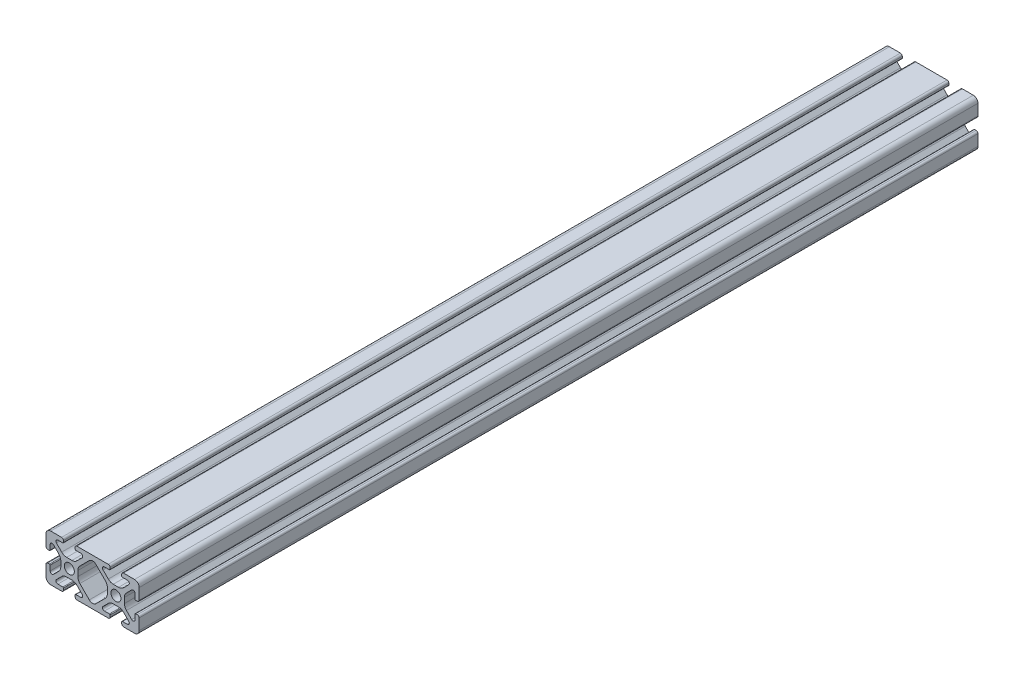
SolidWorks part; units mm, degrees
ref_plane "Alzado" through (0, 0, 0) normal (0, 0, 1) x (1, 0, 0)
ref_plane "Planta" through (0, 0, 0) normal (0, 1, 0) x (1, 0, 0)
ref_plane "Vista lateral" through (0, 0, 0) normal (1, 0, 0) x (0, 0, -1)
ref_plane "Plano1" through (0, 0, 20) normal (0, 0, 1) x (1, 0, 0)
sketch "Croquis1" plane through (0, 0, 20) normal (0, 0, 1) x (1, 0, 0)
  line L0 (32.5, 1.5) -> (32.5, 0.8)
  line L1 (33.3, 0) -> (38, 0)
  line L2 (40, 2) -> (40, 6.7)
  line L3 (39.2, 7.5) -> (38.5, 7.5)
  line L4 (38.2, 7.2) -> (38.2, 5.0824)
  line L5 (36.779, 4.4938) -> (34.5287, 6.7441)
  line L6 (33.65, 8.8654) -> (33.65, 11.1346)
  line L7 (34.5287, 13.2559) -> (36.779, 15.5062)
  line L8 (38.2, 14.9176) -> (38.2, 12.8)
  line L9 (38.5, 12.5) -> (39.2, 12.5)
  line L10 (40, 13.3) -> (40, 18)
  line L11 (38, 20) -> (33.3, 20)
  line L12 (32.5, 19.2) -> (32.5, 18.5)
  line L13 (32.8, 18.2) -> (34.9176, 18.2)
  line L14 (35.5062, 16.779) -> (33.2559, 14.5287)
  line L15 (31.1346, 13.65) -> (28.8654, 13.65)
  line L16 (26.7441, 14.5287) -> (24.4938, 16.779)
  line L17 (25.0824, 18.2) -> (27.2, 18.2)
  line L18 (27.5, 18.5) -> (27.5, 19.2)
  line L19 (26.7, 20) -> (13.3, 20)
  line L20 (12.5, 19.2) -> (12.5, 18.5)
  line L21 (12.8, 18.2) -> (14.9176, 18.2)
  line L22 (15.5062, 16.779) -> (13.2559, 14.5287)
  line L23 (11.1346, 13.65) -> (8.8654, 13.65)
  line L24 (6.7441, 14.5287) -> (4.4938, 16.779)
  line L25 (5.0824, 18.2) -> (7.2, 18.2)
  line L26 (7.5, 18.5) -> (7.5, 19.2)
  line L27 (6.7, 20) -> (2, 20)
  line L28 (0, 18) -> (0, 13.3)
  line L29 (0.8, 12.5) -> (1.5, 12.5)
  line L30 (1.8, 12.8) -> (1.8, 14.9176)
  line L31 (3.221, 15.5062) -> (5.4713, 13.2559)
  line L32 (6.35, 11.1346) -> (6.35, 8.8654)
  line L33 (5.4713, 6.7441) -> (3.221, 4.4938)
  line L34 (1.8, 5.0824) -> (1.8, 7.2)
  line L35 (1.5, 7.5) -> (0.8, 7.5)
  line L36 (0, 6.7) -> (0, 2)
  line L37 (2, 0) -> (6.7, 0)
  line L38 (7.5, 0.8) -> (7.5, 1.5)
  line L39 (7.2, 1.8) -> (5.0824, 1.8)
  line L40 (4.4938, 3.221) -> (6.7441, 5.4713)
  line L41 (8.8654, 6.35) -> (11.1346, 6.35)
  line L42 (13.2559, 5.4713) -> (15.5062, 3.221)
  line L43 (14.9176, 1.8) -> (12.8, 1.8)
  line L44 (12.5, 1.5) -> (12.5, 0.8)
  line L45 (13.3, 0) -> (26.7, 0)
  line L46 (27.5, 0.8) -> (27.5, 1.5)
  line L47 (27.2, 1.8) -> (25.0824, 1.8)
  line L48 (24.4938, 3.221) -> (26.7441, 5.4713)
  line L49 (28.8654, 6.35) -> (31.1346, 6.35)
  line L50 (33.2559, 5.4713) -> (35.5062, 3.221)
  line L51 (34.9176, 1.8) -> (32.8, 1.8)
  line L52 (18.5858, 2.687) -> (14.5287, 6.7441)
  line L53 (13.65, 8.8654) -> (13.65, 11.1346)
  line L54 (14.5287, 13.2559) -> (18.5858, 17.313)
  line L55 (21.4142, 17.313) -> (25.4713, 13.2559)
  line L56 (26.35, 11.1346) -> (26.35, 8.8654)
  line L57 (25.4713, 6.7441) -> (21.4142, 2.687)
  arc A0 (32.8, 1.8) -> (32.5, 1.5) centre (32.8, 1.5) ccw
  arc A1 (32.5, 0.8) -> (33.3, 0) centre (33.3, 0.8) ccw
  arc A2 (38, 0) -> (40, 2) centre (38, 2) ccw
  arc A3 (40, 6.7) -> (39.2, 7.5) centre (39.2, 6.7) ccw
  arc A4 (38.5, 7.5) -> (38.2, 7.2) centre (38.5, 7.2) ccw
  arc A5 (38.2, 5.0824) -> (36.779, 4.4938) centre (37.3676, 5.0824) cw
  arc A6 (34.5287, 6.7441) -> (33.65, 8.8654) centre (36.65, 8.8654) cw
  arc A7 (33.65, 11.1346) -> (34.5287, 13.2559) centre (36.65, 11.1346) cw
  arc A8 (36.779, 15.5062) -> (38.2, 14.9176) centre (37.3676, 14.9176) cw
  arc A9 (38.2, 12.8) -> (38.5, 12.5) centre (38.5, 12.8) ccw
  arc A10 (39.2, 12.5) -> (40, 13.3) centre (39.2, 13.3) ccw
  arc A11 (40, 18) -> (38, 20) centre (38, 18) ccw
  arc A12 (33.3, 20) -> (32.5, 19.2) centre (33.3, 19.2) ccw
  arc A13 (32.5, 18.5) -> (32.8, 18.2) centre (32.8, 18.5) ccw
  arc A14 (34.9176, 18.2) -> (35.5062, 16.779) centre (34.9176, 17.3676) cw
  arc A15 (33.2559, 14.5287) -> (31.1346, 13.65) centre (31.1346, 16.65) cw
  arc A16 (28.8654, 13.65) -> (26.7441, 14.5287) centre (28.8654, 16.65) cw
  arc A17 (24.4938, 16.779) -> (25.0824, 18.2) centre (25.0824, 17.3676) cw
  arc A18 (27.2, 18.2) -> (27.5, 18.5) centre (27.2, 18.5) ccw
  arc A19 (27.5, 19.2) -> (26.7, 20) centre (26.7, 19.2) ccw
  arc A20 (13.3, 20) -> (12.5, 19.2) centre (13.3, 19.2) ccw
  arc A21 (12.5, 18.5) -> (12.8, 18.2) centre (12.8, 18.5) ccw
  arc A22 (14.9176, 18.2) -> (15.5062, 16.779) centre (14.9176, 17.3676) cw
  arc A23 (13.2559, 14.5287) -> (11.1346, 13.65) centre (11.1346, 16.65) cw
  arc A24 (8.8654, 13.65) -> (6.7441, 14.5287) centre (8.8654, 16.65) cw
  arc A25 (4.4938, 16.779) -> (5.0824, 18.2) centre (5.0824, 17.3676) cw
  arc A26 (7.2, 18.2) -> (7.5, 18.5) centre (7.2, 18.5) ccw
  arc A27 (7.5, 19.2) -> (6.7, 20) centre (6.7, 19.2) ccw
  arc A28 (2, 20) -> (0, 18) centre (2, 18) ccw
  arc A29 (0, 13.3) -> (0.8, 12.5) centre (0.8, 13.3) ccw
  arc A30 (1.5, 12.5) -> (1.8, 12.8) centre (1.5, 12.8) ccw
  arc A31 (1.8, 14.9176) -> (3.221, 15.5062) centre (2.6324, 14.9176) cw
  arc A32 (5.4713, 13.2559) -> (6.35, 11.1346) centre (3.35, 11.1346) cw
  arc A33 (6.35, 8.8654) -> (5.4713, 6.7441) centre (3.35, 8.8654) cw
  arc A34 (3.221, 4.4938) -> (1.8, 5.0824) centre (2.6324, 5.0824) cw
  arc A35 (1.8, 7.2) -> (1.5, 7.5) centre (1.5, 7.2) ccw
  arc A36 (0.8, 7.5) -> (0, 6.7) centre (0.8, 6.7) ccw
  arc A37 (0, 2) -> (2, 0) centre (2, 2) ccw
  arc A38 (6.7, 0) -> (7.5, 0.8) centre (6.7, 0.8) ccw
  arc A39 (7.5, 1.5) -> (7.2, 1.8) centre (7.2, 1.5) ccw
  arc A40 (5.0824, 1.8) -> (4.4938, 3.221) centre (5.0824, 2.6324) cw
  arc A41 (6.7441, 5.4713) -> (8.8654, 6.35) centre (8.8654, 3.35) cw
  arc A42 (11.1346, 6.35) -> (13.2559, 5.4713) centre (11.1346, 3.35) cw
  arc A43 (15.5062, 3.221) -> (14.9176, 1.8) centre (14.9176, 2.6324) cw
  arc A44 (12.8, 1.8) -> (12.5, 1.5) centre (12.8, 1.5) ccw
  arc A45 (12.5, 0.8) -> (13.3, 0) centre (13.3, 0.8) ccw
  arc A46 (26.7, 0) -> (27.5, 0.8) centre (26.7, 0.8) ccw
  arc A47 (27.5, 1.5) -> (27.2, 1.8) centre (27.2, 1.5) ccw
  arc A48 (25.0824, 1.8) -> (24.4938, 3.221) centre (25.0824, 2.6324) cw
  arc A49 (26.7441, 5.4713) -> (28.8654, 6.35) centre (28.8654, 3.35) cw
  arc A50 (31.1346, 6.35) -> (33.2559, 5.4713) centre (31.1346, 3.35) cw
  arc A51 (35.5062, 3.221) -> (34.9176, 1.8) centre (34.9176, 2.6324) cw
  circle A52 centre (10, 10) radius 2.15
  circle A53 centre (30, 10) radius 2.15
  arc A54 (21.4142, 2.687) -> (18.5858, 2.687) centre (20, 4.1012) cw
  arc A55 (14.5287, 6.7441) -> (13.65, 8.8654) centre (16.65, 8.8654) cw
  arc A56 (13.65, 11.1346) -> (14.5287, 13.2559) centre (16.65, 11.1346) cw
  arc A57 (18.5858, 17.313) -> (21.4142, 17.313) centre (20, 15.8988) cw
  arc A58 (25.4713, 13.2559) -> (26.35, 11.1346) centre (23.35, 11.1346) cw
  arc A59 (26.35, 8.8654) -> (25.4713, 6.7441) centre (23.35, 8.8654) cw
extrude "Saliente-Extruir1" add sketch "Croquis1" against normal blind 360
